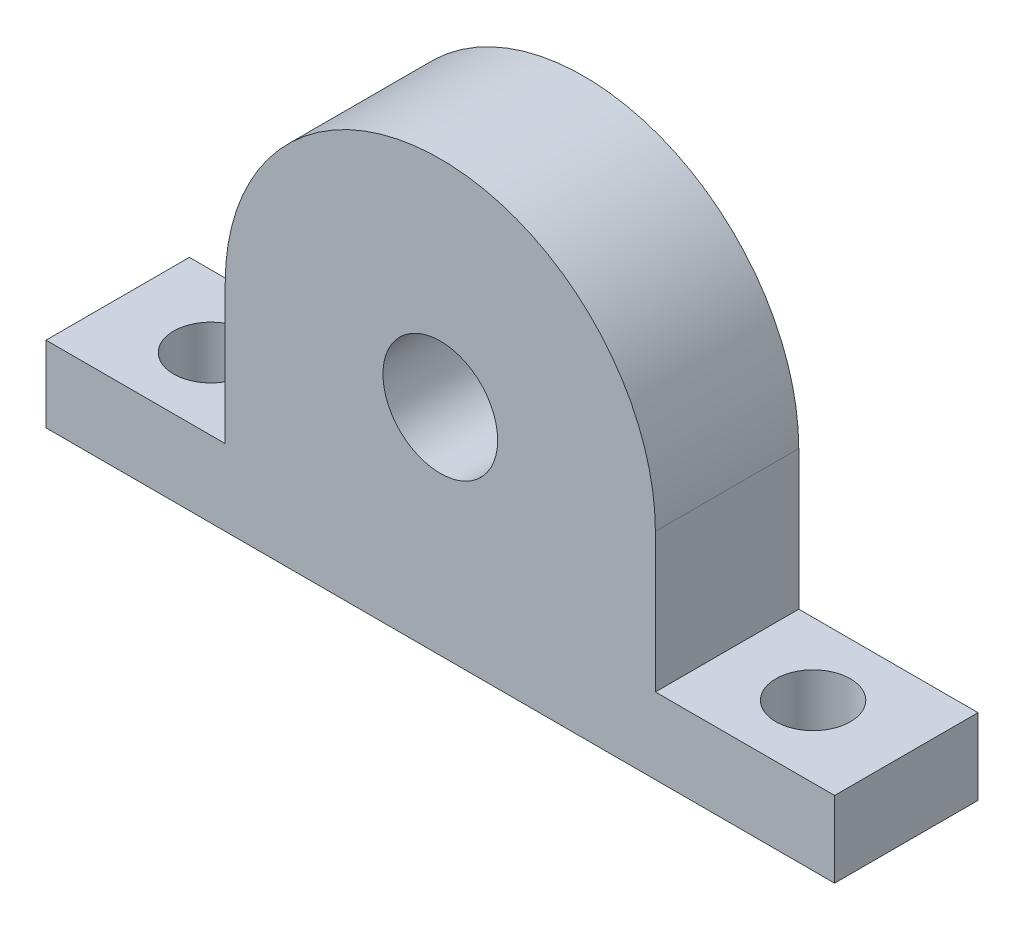
SolidWorks part; units mm, degrees
ref_plane "前视基准面" through (0, 0, 0) normal (0, 0, 1) x (1, 0, 0)
ref_plane "上视基准面" through (0, 0, 0) normal (0, 1, 0) x (1, 0, 0)
ref_plane "右视基准面" through (0, 0, 0) normal (1, 0, 0) x (0, 0, -1)
sketch "草图1" plane through (0, 0, 0) normal (0, 0, 1) x (1, 0, 0)
  line L0 (-27.5, -15) -> (27.5, -15)
  line L1 (15, 0) -> (15, -9.7)
  line L2 (27.5, -15) -> (27.5, -9.7)
  line L3 (27.5, -9.7) -> (15, -9.7)
  line L4 (0, 15) -> (0, -15) construction
  line L5 (-15, 0) -> (-15, -9.7)
  line L6 (-27.5, -9.7) -> (-15, -9.7)
  line L7 (-27.5, -15) -> (-27.5, -9.7)
  circle A0 centre (0, 0) radius 4
  arc A1 (15, 0) -> (-15, 0) centre (0, 0) ccw
  dimension "D1" = 5.3
  dimension "D3" = 30
  dimension "D4" = 8
  dimension "D2" = 27.5
extrude "凸台-拉伸1" add sketch "草图1" along normal blind 10
sketch "草图2" plane through (0, -9.7, 0) normal (0, 1, 0) x (1, 0, 0)
  line L0 (0, 0) -> (0, -10) construction
  line L1 (-15, -10) -> (15, -10) construction
  line L2 (27.5, -10) -> (15, -10) construction
  circle A0 centre (21, -5) radius 2.6
  circle A1 centre (-21, -5) radius 2.6
  dimension "D1" = 21
  dimension "D3" = 5.2
  dimension "D2" = 5
extrude "切除-拉伸1" cut sketch "草图2" against normal blind 10
